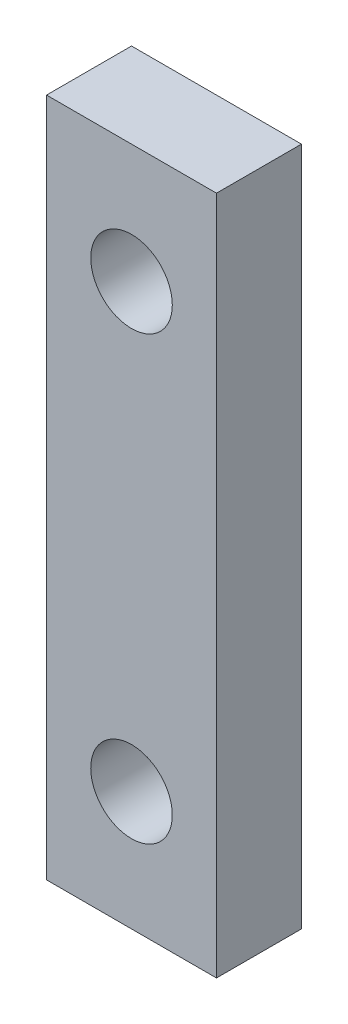
SolidWorks part; units mm, degrees
ref_plane "Front Plane" through (0, 0, 0) normal (0, 0, 1) x (1, 0, 0)
ref_plane "Top Plane" through (0, 0, 0) normal (0, 1, 0) x (1, 0, 0)
ref_plane "Right Plane" through (0, 0, 0) normal (1, 0, 0) x (0, 0, -1)
sketch "Sketch1" plane through (0, 0, 0) normal (0, 0, 1) x (1, 0, 0)
  line L1 (-5, 20) -> (5, 20)
  line L2 (-5, 20) -> (-5, -20)
  line L3 (-5, -20) -> (5, -20)
  line L4 (5, 20) -> (5, -20)
  line L5 (0, -20) -> (0, 20) construction
  line L6 (-5, 0) -> (5, 0) construction
  circle A0 centre (0, 13) radius 2.4
  circle A1 centre (0, -13) radius 2.4
  point P0 (0, 0)
  dimension "D3" = 4.8
  dimension "D1" = 40
  dimension "D2" = 10
  dimension "D4" = 13
extrude "Boss-Extrude1" add sketch "Sketch1" along normal blind 5
